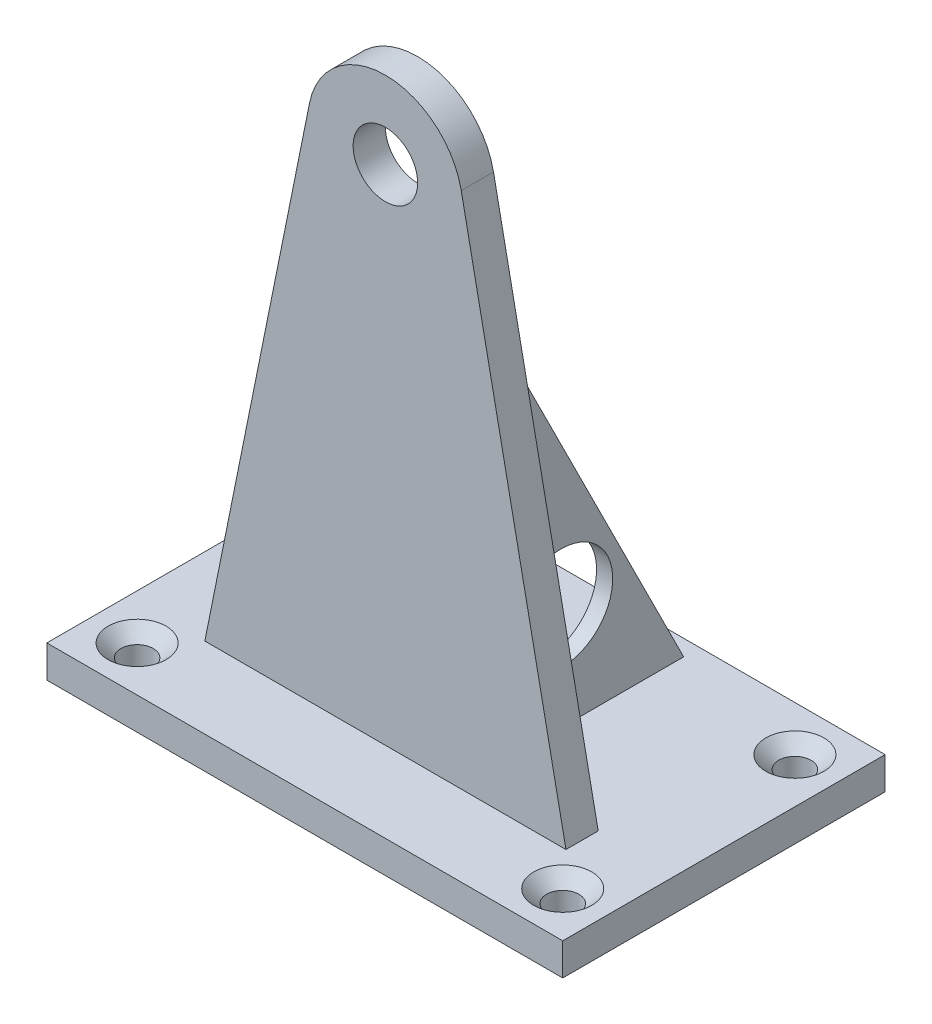
SolidWorks part; units mm, degrees
material "AISI 1020"
ref_plane "Front Plane" through (0, 0, 0) normal (0, 0, 1) x (1, 0, 0)
ref_plane "Top Plane" through (0, 0, 0) normal (0, 1, 0) x (1, 0, 0)
ref_plane "Right Plane" through (0, 0, 0) normal (1, 0, 0) x (0, 0, -1)
sketch "Sketch2" plane through (0, 0, 0) normal (0, 1, 0) x (1, 0, 0)
  line L1 (-40, -25) -> (40, -25)
  line L2 (-40, -25) -> (-40, 25)
  line L3 (-40, 25) -> (40, 25)
  line L4 (40, -25) -> (40, 25)
  line L5 (-40, -25) -> (40, 25) construction
  line L6 (-40, 25) -> (40, -25) construction
  point P0 (0, 0)
  dimension "D1" = 80
  dimension "D2" = 50
extrude "Boss-Extrude1" add sketch "Sketch2" along normal blind 5
sketch "Sketch3" plane through (0, 5, 0) normal (0, 1, 0) x (1, 0, 0)
  line L0 (0, 25) -> (0, -25) construction
  line L1 (40, 25) -> (-40, 25) construction
  line L2 (-40, -25) -> (40, -25) construction
  line L3 (-40, 0) -> (40, 0) construction
  line L4 (-40, 25) -> (-40, -25) construction
  line L5 (40, -25) -> (40, 25) construction
  circle A0 centre (-33, 18) radius 2.5
  circle A1 centre (-33, -18) radius 2.5
  circle A2 centre (33, -18) radius 2.5
  circle A3 centre (33, 18) radius 2.5
  point P14 (0, 0)
  dimension "D1" = 5
  dimension "D2" = 33
  dimension "D3" = 18
ref_plane "Plane1" through (0, 0, 10) normal (0, 0, 1) x (1, 0, 0)
sketch "Sketch4" plane through (0, 0, 10) normal (0, 0, 1) x (1, 0, 0)
  line L0 (0, 5) -> (-28, 5)
  line L1 (-40, 5) -> (40, 5) construction
  line L2 (-28, 5) -> (-11.7624, 85.3762)
  line L3 (0, 5) -> (0, 83)
  line L4 (0, 83) -> (0, 95)
  circle A1 centre (0, 83) radius 12 construction
  arc A2 (-11.7624, 85.3762) -> (0, 95) centre (0, 83) cw
  dimension "D1" = 28
  dimension "D2" = 12
  dimension "D3" = 78
extrude "Boss-Extrude2" add sketch "Sketch4" against normal mid plane 5
ref_plane "Plane2" through (-10, 0, 0) normal (1, 0, 0) x (0, 0, -1)
sketch "Sketch6" plane through (-10, 0, 0) normal (1, 0, 0) x (0, 0, -1)
  line L0 (-7.5, 65) -> (22.5, 5)
  line L1 (-7.5, 5) -> (-7.5, 95) construction
  line L2 (25, 5) -> (-25, 5) construction
  dimension "D1" = 60
  dimension "D2" = 30
rib "Rib1" sketch "Sketch6" sketch "Sketch6" thickness 2.5 extrusion direction parallel to sketch draft on no parameters "D1"=2.5
sketch "Sketch7" plane through (-10, 0, 0) normal (1, 0, 0) x (0, 0, -1)
  line L0 (-7.5, 65) -> (-7.5, 5) construction
  line L1 (25, 5) -> (-25, 5) construction
  circle A0 centre (3.5, 21) radius 8
  point P4 (0, 0)
  dimension "D1" = 16
  dimension "D2" = 11
  dimension "D3" = 16
extrude "Cut-Extrude1" cut sketch "Sketch7" against normal mid plane 5
mirror "Mirror2" about plane through (0, 83, 7.5) normal (1, 0, 0) of "Cut-Extrude1", "Boss-Extrude2", "Rib1"
extrude "Cut-Extrude2" cut sketch "Sketch3" against normal blind 5
chamfer "Chamfer1" distance 2 angle 45 4 edges at (33, 5, -20.5) (-33, 5, -15.5) (-33, 5, 15.5) (33, 5, 20.5)
sketch "Sketch8" plane through (0, 0, 10) normal (0, 0, 1) x (1, 0, 0)
  circle A0 centre (0, 83) radius 5
  dimension "D1" = 10
extrude "Cut-Extrude3" cut sketch "Sketch8" against normal mid plane 5
